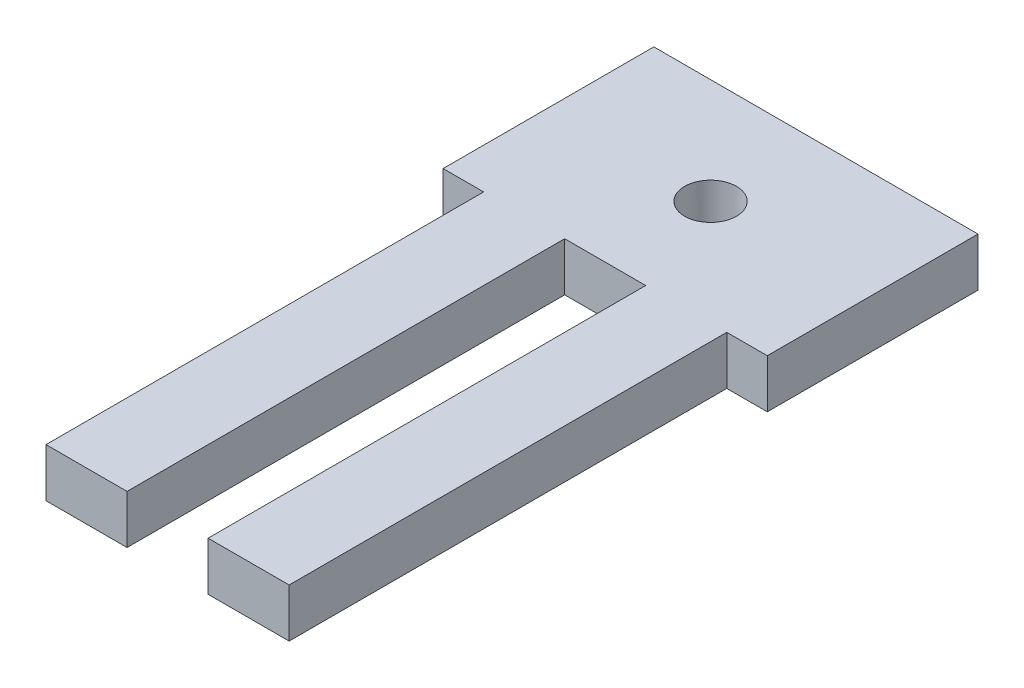
SolidWorks part; units mm, degrees
ref_plane "Front Plane" through (0, 0, 0) normal (0, 0, 1) x (1, 0, 0)
ref_plane "Top Plane" through (0, 0, 0) normal (0, 1, 0) x (1, 0, 0)
ref_plane "Right Plane" through (0, 0, 0) normal (1, 0, 0) x (0, 0, -1)
sketch "Sketch1" plane through (0, 0, 0) normal (0, 1, 0) x (1, 0, 0)
  line L1 (0, 0) -> (20, 0)
  line L2 (0, 0) -> (0, 40)
  line L3 (0, 40) -> (20, 40)
  line L4 (20, 0) -> (20, 40)
  dimension "D1" = 40
  dimension "D2" = 20
extrude "Boss-Extrude1" add sketch "Sketch1" along normal blind 3
sketch "Sketch2" plane through (0, 3, 0) normal (0, 1, 0) x (1, 0, 0)
  line L0 (0, 0) -> (20, 0) construction
  line L1 (0, 27) -> (2.5, 27)
  line L2 (0, 27) -> (0, 0)
  line L3 (0, 0) -> (2.5, 0)
  line L4 (2.5, 27) -> (2.5, 0)
  line L6 (0, 40) -> (0, 0) construction
  dimension "D1" = 27
  dimension "D2" = 2.5
extrude "Cut-Extrude1" cut sketch "Sketch2" against normal up to next (3 mm away)
ref_plane "Plane1" through (10, 0, 0) normal (-1, 0, 0) x (0, 0, 1)
mirror "Mirror1" about plane through (10, 0, 0) normal (-1, 0, 0) of "Cut-Extrude1"
sketch "Sketch3" plane through (0, 3, 0) normal (0, 1, 0) x (1, 0, 0)
  line L0 (10, 1.65) -> (10, -1.65) construction
  line L1 (2.5, 27) -> (0, 27) construction
  circle A0 centre (10, 33.5) radius 1.6
  dimension "D1" = 3.2
  dimension "D2" = 6.5
extrude "Cut-Extrude2" cut sketch "Sketch3" against normal through all both and the other way through all
sketch "Sketch4" plane through (0, 3, 0) normal (0, 1, 0) x (1, 0, 0)
  line L0 (2.5, 0) -> (17.5, 0) construction
  line L1 (12.5, 0) -> (7.5, 0)
  line L2 (12.5, 0) -> (12.5, 27)
  line L3 (12.5, 27) -> (7.5, 27)
  line L4 (7.5, 0) -> (7.5, 27)
  line L5 (10, 1.65) -> (10, -1.65) construction
  line L6 (2.5, 27) -> (0, 27) construction
  point P6 (10, 27)
  point P9 (0, 0)
  dimension "D2" = 5
extrude "Cut-Extrude3" cut sketch "Sketch4" against normal through all both and the other way through all
